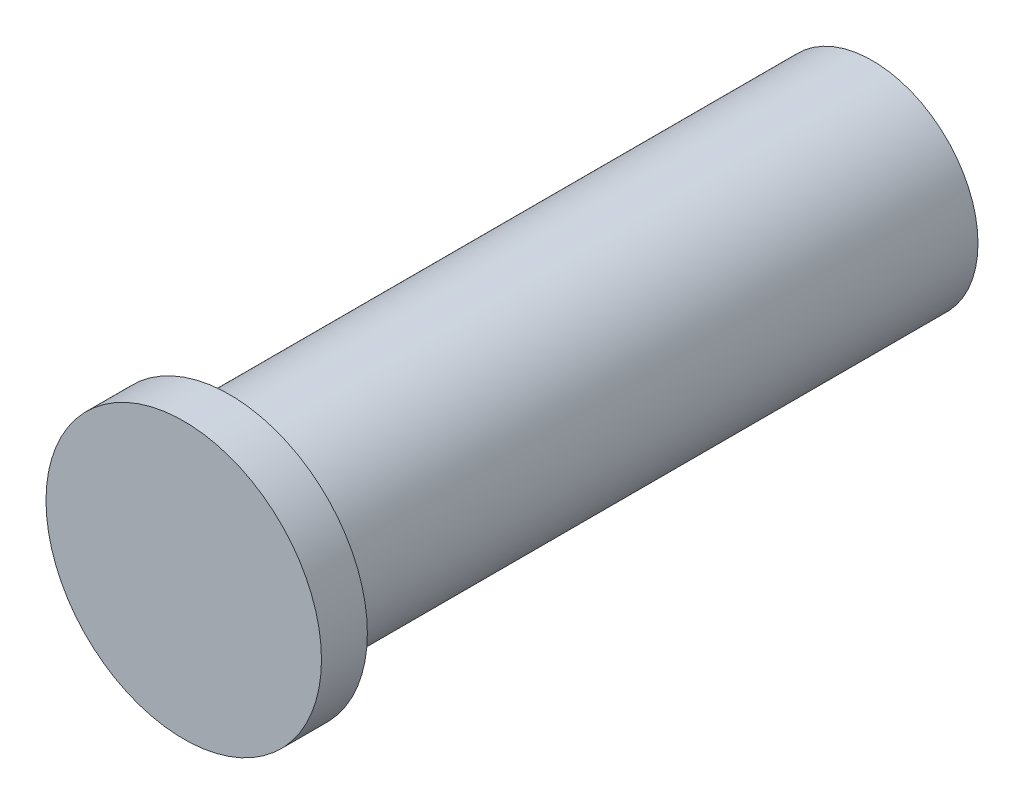
SolidWorks part; units mm, degrees
ref_plane "Front Plane" through (0, 0, 0) normal (0, 0, 1) x (1, 0, 0)
ref_plane "Top Plane" through (0, 0, 0) normal (0, 1, 0) x (1, 0, 0)
ref_plane "Right Plane" through (0, 0, 0) normal (1, 0, 0) x (0, 0, -1)
sketch "Sketch1" plane through (0, 0, 0) normal (0, 0, 1) x (1, 0, 0)
  circle A0 centre (0, 0) radius 2.3
  dimension "D1" = 4.6
extrude "Boss-Extrude1" add sketch "Sketch1" along normal blind 14
sketch "Sketch2" plane through (0, 0, 14) normal (0, 0, 1) x (1, 0, 0)
  circle A0 centre (0, 0) radius 3
  dimension "D1" = 6
extrude "Boss-Extrude2" add sketch "Sketch2" along normal blind 1
